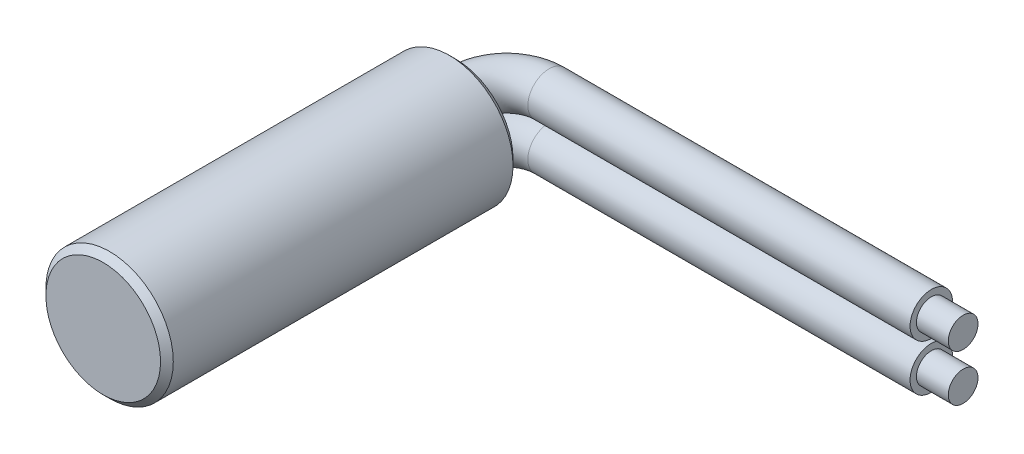
SolidWorks part; units mm, degrees
ref_plane "Front Plane" through (0, 0, 0) normal (0, 0, 1) x (1, 0, 0)
ref_plane "Top Plane" through (0, 0, 0) normal (0, 1, 0) x (1, 0, 0)
ref_plane "Right Plane" through (0, 0, 0) normal (1, 0, 0) x (0, 0, -1)
sketch "Sketch1" plane through (0, 0, 0) normal (0, 0, 1) x (1, 0, 0)
  circle A0 centre (0, 0) radius 3
  dimension "D1" = 6
extrude "Casing" add sketch "Sketch1" along normal blind 16.6
chamfer "Casing Chamfer" distance 0.3 angle 45 2 edges at (3, 0, 0) (3, 0, 16.6)
sketch "Sketch2" plane through (0, 0, 0) normal (0, 1, 0) x (1, 0, 0)
  line L0 (0, 0) -> (0, 0.4)
  line L1 (2, 2.4) -> (20, 2.4)
  arc A0 (2, 2.4) -> (0, 0.4) centre (2, 0.4) ccw
  point P6 (0, 2.4)
  dimension "D3" = 2
  dimension "D1" = 2.4
  dimension "D2" = 20
sketch "Sketch3" plane through (0, 0, 0) normal (0, 0, -1) x (-1, 0, 0)
  line L0 (0, 0) -> (0, 1.1) construction
  line L1 (0, 0) -> (0, -1.1) construction
  circle A1 centre (0, -1.1) radius 1
  circle A2 centre (0, 1.1) radius 1
  dimension "D2" = 2
  dimension "D1" = 2.2
sweep "Wire" add profiles "Sketch3" path "Sketch2"
sketch "Sketch4" plane through (20, 0, 0) normal (1, 0, 0) x (0, 0, -1)
  circle A2 centre (2.4, 1.1) radius 0.7
  circle A3 centre (2.4, 1.1) radius 0.7
  circle A5 centre (2.4, -1.1) radius 0.7
  circle A6 centre (2.4, -1.1) radius 0.7
  dimension "D1" = 0.3
  dimension "D2" = 0.3
extrude "Exposed Wire" add sketch "Sketch4" along normal blind 1.5
